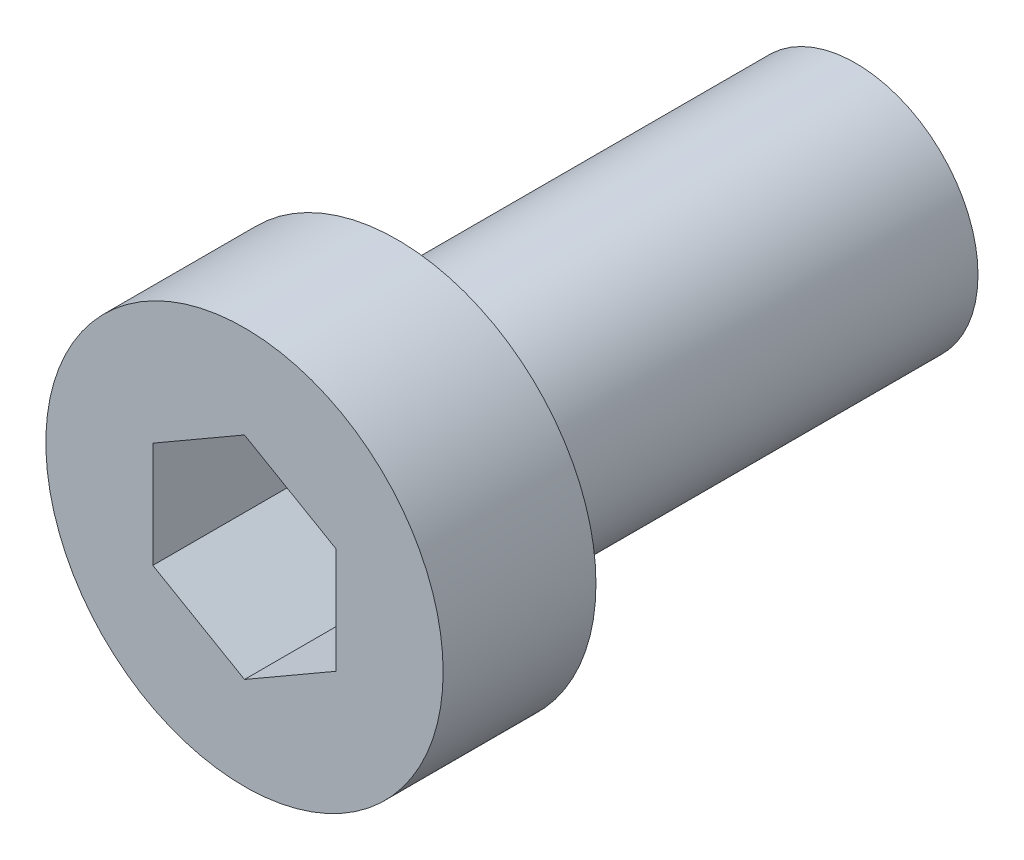
SolidWorks part; units mm, degrees
ref_plane "Plane1" through (0, 0, 0) normal (0, 0, 1) x (1, 0, 0)
ref_plane "Plane2" through (0, 0, 0) normal (0, 1, 0) x (1, 0, 0)
ref_plane "Plane3" through (0, 0, 0) normal (1, 0, 0) x (0, 0, -1)
sketch "Sketch1" plane through (0, 0, 0) normal (0, 0, 1) x (1, 0, 0)
  circle A0 centre (0, 0) radius 6.5
  dimension "d2 Hoveddiameter" = 13
extrude "Base-Extrude" add sketch "Sketch1" along normal blind 5
sketch "Sketch2" plane through (0, 0, 0) normal (0, 0, -1) x (-1, 0, 0)
  circle A0 centre (0, 0) radius 4
  dimension "M Gevind" = 8
extrude "Boss-Extrude1" add sketch "Sketch2" along normal blind 15
sketch "Sketch3" plane through (0, 0, 5) normal (0, 0, 1) x (1, 0, 0)
  line L1 (0, 3.4641) -> (-3, 1.7321)
  line L2 (-3, 1.7321) -> (-3, -1.7321)
  line L3 (-3, -1.7321) -> (0, -3.4641)
  line L4 (0, -3.4641) -> (3, -1.7321)
  line L5 (3, -1.7321) -> (3, 1.7321)
  line L6 (3, 1.7321) -> (0, 3.4641)
  circle A0 centre (0, 0) radius 3 construction
  dimension "s Nøglevidde" = 6
extrude "Cut-Extrude1" cut sketch "Sketch3" against normal blind 5
